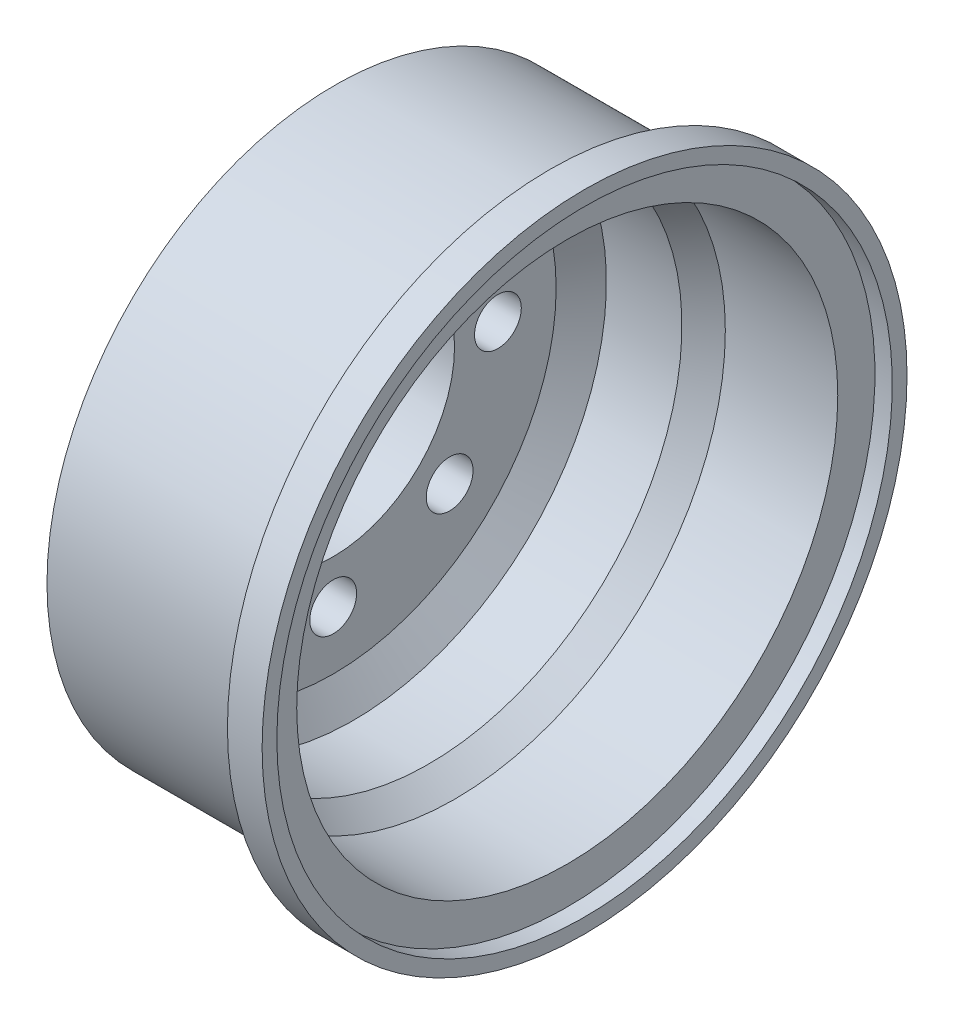
SolidWorks part; units mm, degrees
ref_plane "Front Plane" through (0, 0, 0) normal (0, 0, 1) x (1, 0, 0)
ref_plane "Top Plane" through (0, 0, 0) normal (0, 1, 0) x (1, 0, 0)
ref_plane "Right Plane" through (0, 0, 0) normal (1, 0, 0) x (0, 0, -1)
sketch "Sketch1" plane through (0, 0, 0) normal (0, 0, 1) x (1, 0, 0)
  line L0 (-25, 0) -> (25, 0) construction
  line L1 (-5.2981, 7) -> (-5.2981, 12.7158)
  line L2 (-5.2981, 12.7158) -> (-2.7086, 16.6)
  line L3 (-2.7086, 16.6) -> (9.7014, 16.6)
  line L4 (9.7014, 16.6) -> (9.7014, 18.6)
  line L5 (9.7014, 18.6) -> (11.7014, 18.6)
  line L6 (11.7014, 18.6) -> (11.7014, 17.75)
  line L7 (2.7156, 14.6) -> (-1.6383, 14.6)
  line L8 (-1.6383, 14.6) -> (-2.7981, 12.8603)
  line L9 (-2.7981, 12.8603) -> (-2.7981, 7)
  line L11 (11.7014, 17.75) -> (10.7014, 17.75)
  line L12 (10.7014, 17.75) -> (10.7014, 15.6046)
  line L13 (-5.2981, 7) -> (-2.7981, 7)
  line L14 (2.7156, 14.6) -> (4.2156, 15.6046)
  line L15 (4.2156, 15.6046) -> (10.7014, 15.6046)
  dimension "D1" = 50
  dimension "D2" = 25
  dimension "D3" = 33.2
  dimension "D4" = 2
  dimension "D5" = 2
  dimension "D6" = 2
  dimension "D7" = 2
  dimension "D8" = 2.5
  dimension "D9" = 12.41
  dimension "D10" = 0.85
  dimension "D11" = 1
  dimension "D12" = 14
  dimension "D13" = 1.0046
  dimension "D14" = 1.5
revolve "Revolve1" add sketch "Sketch1" angle 360 about L0
sketch "Sketch2" plane through (-2.7981, 0, 0) normal (1, 0, 0) x (0, 0, -1)
  circle A0 centre (0, 0) radius 12.8603 construction
  circle A1 centre (0, 0) radius 12.8603 construction
  circle A2 centre (0, 0) radius 9.5 construction
  circle A3 centre (0, 9.5) radius 1.35
  circle A4 centre (6.7175, 6.7175) radius 1.35
  circle A5 centre (9.5, 0) radius 1.35
  circle A6 centre (6.7175, -6.7175) radius 1.35
  circle A7 centre (0, -9.5) radius 1.35
  circle A8 centre (-6.7175, -6.7175) radius 1.35
  circle A9 centre (-9.5, 0) radius 1.35
  circle A10 centre (-6.7175, 6.7175) radius 1.35
  point P23 (0, 0)
  dimension "D1" = 19
  dimension "D2" = 2.7
  dimension "D3" = 8
extrude "Cut-Extrude1" cut sketch "Sketch2" against normal blind 10
